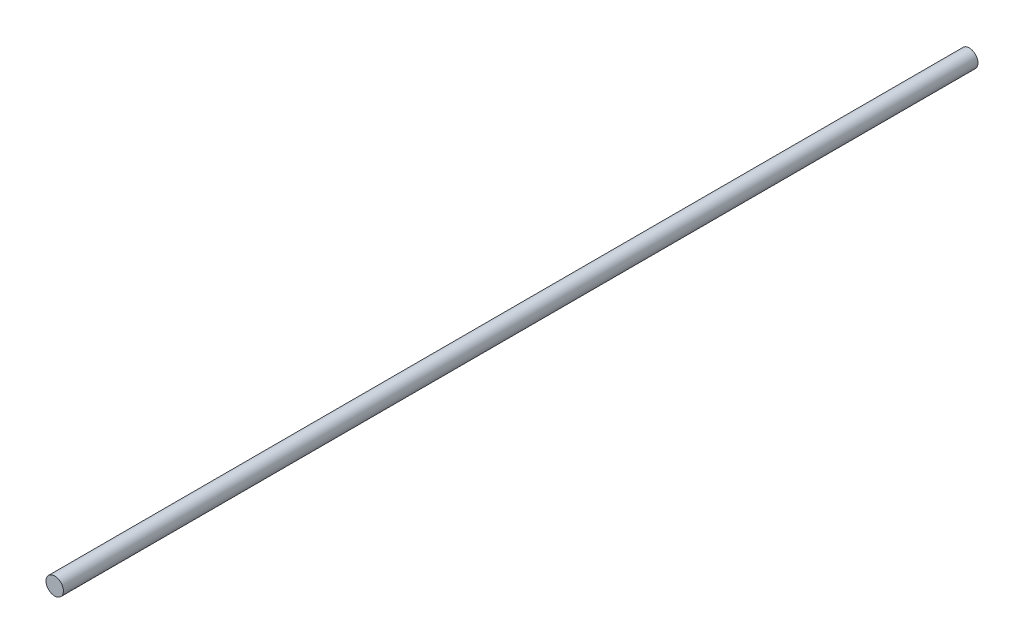
SolidWorks part; units mm, degrees
ref_plane "Front Plane" through (0, 0, 0) normal (0, 0, 1) x (1, 0, 0)
ref_plane "Top Plane" through (0, 0, 0) normal (0, 1, 0) x (1, 0, 0)
ref_plane "Right Plane" through (0, 0, 0) normal (1, 0, 0) x (0, 0, -1)
sketch "Esboço1" plane through (0, 0, 0) normal (0, 0, 1) x (1, 0, 0)
  circle A0 centre (-48.8753, 81.4072) radius 4
  dimension "D1" = 8
extrude "Ressalto-extrusão1" add sketch "Esboço1" along normal blind 420 contours A0
